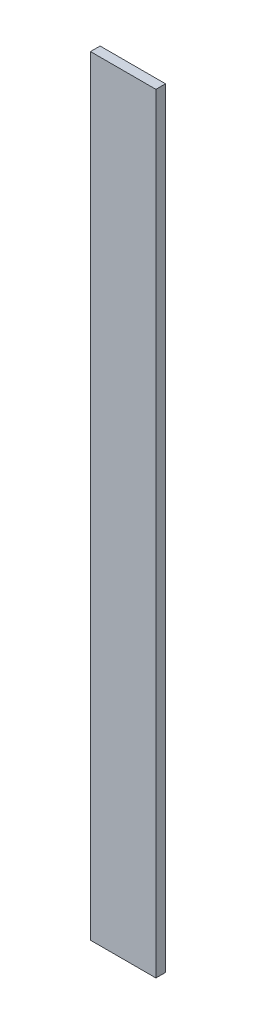
SolidWorks part; units mm, degrees
ref_plane "Front Plane" through (0, 0, 0) normal (0, 0, 1) x (1, 0, 0)
ref_plane "Top Plane" through (0, 0, 0) normal (0, 1, 0) x (1, 0, 0)
ref_plane "Right Plane" through (0, 0, 0) normal (1, 0, 0) x (0, 0, -1)
sketch "Sketch1" plane through (0, 0, 0) normal (0, 1, 0) x (1, 0, 0)
  line L1 (0, 0) -> (43.18, 0)
  line L2 (0, 0) -> (0, 6.35)
  line L3 (0, 6.35) -> (43.18, 6.35)
  line L4 (43.18, 0) -> (43.18, 6.35)
  dimension "D1" = 43.18
  dimension "D2" = 6.35
extrude "Boss-Extrude1" add sketch "Sketch1" along normal blind 508
